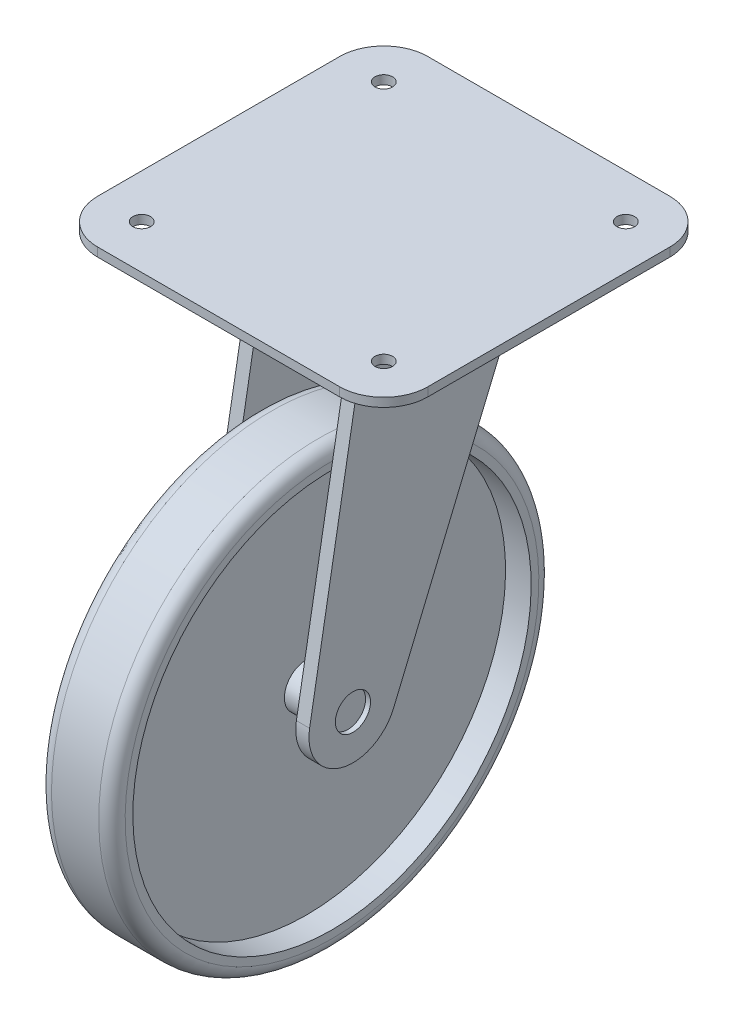
SolidWorks part; units mm, degrees
ref_plane "Front Plane" through (0, 0, 0) normal (0, 0, 1) x (1, 0, 0)
ref_plane "Top Plane" through (0, 0, 0) normal (0, 1, 0) x (1, 0, 0)
ref_plane "Right Plane" through (0, 0, 0) normal (1, 0, 0) x (0, 0, -1)
sketch "Sketch1" plane through (0, 0, 0) normal (0, 1, 0) x (1, 0, 0)
  line L0 (0, -55) -> (0, 55) construction
  line L1 (-37.5, 37.5) -> (37.5, 37.5)
  line L2 (-37.5, 37.5) -> (-37.5, -37.5)
  line L3 (-37.5, -37.5) -> (37.5, -37.5)
  line L4 (37.5, 37.5) -> (37.5, -37.5)
  line L5 (-55, 0) -> (55, 0) construction
  circle A0 centre (27.5, 27.5) radius 2
  circle A1 centre (27.5, -27.5) radius 2
  circle A2 centre (-27.5, -27.5) radius 2
  circle A3 centre (-27.5, 27.5) radius 2
  dimension "D4" = 10
  dimension "D5" = 10
  dimension "D6" = 4
  dimension "D1" = 75
  dimension "D2" = 37.5
  dimension "D3" = 37.5
  dimension "D7" = 4
extrude "Boss-Extrude1" add sketch "Sketch1" against normal blind 2
fillet "Fillet1" radius 10 4 edges at (-37.5, -1, 37.5) (-37.5, -1, -37.5) (37.5, -1, -37.5) (37.5, -1, 37.5)
sketch "Sketch2" plane through (0, -2, 0) normal (0, -1, 0) x (1, 0, 0)
  circle A0 centre (0, 0) radius 21.2583
  circle A1 centre (0, 0) radius 25
  dimension "D1" = 50
extrude "Boss-Extrude2" add sketch "Sketch2" along normal blind 6
sketch "Sketch3" plane through (0, 0, 0) normal (1, 0, 0) x (0, 0, -1)
  line L0 (0, 4.4) -> (0, -4.4) construction
  line L1 (41.25, 0) -> (-41.25, 0) construction
  line L2 (-17.5495, -8) -> (20.9636, -8)
  line L3 (-25, -8) -> (25, -8) construction
  line L4 (20.9636, -8) -> (-10.7749, -83.8596)
  line L5 (-17.5495, -8) -> (-29.8502, -78.2759)
  circle A0 centre (-20, -80) radius 50 construction
  arc A1 (-29.8502, -78.2759) -> (-10.7749, -83.8596) centre (-20, -80) ccw
  circle A2 centre (-20, -80) radius 4
  dimension "D1" = 100
  dimension "D4" = 8
  dimension "D5" = 20
  dimension "D2" = 20
  dimension "D3" = 80
extrude "Boss-Extrude3" add sketch "Sketch3" along normal blind 3 from offset 10
mirror "Mirror1" about plane through (0, 0, 0) normal (1, 0, 0) of "Boss-Extrude3"
ref_plane "Plane1" through (0, 0, 20) normal (0, 0, 1) x (1, 0, 0)
sketch "Sketch4" plane through (0, 0, 20) normal (0, 0, 1) x (1, 0, 0)
  line L0 (-10, -80) -> (11.8719, -80) construction
  line L1 (-13, -80) -> (-10, -80) construction
  line L2 (-10, -90) -> (-10, -78.2759) construction
  line L3 (13, -80) -> (10, -80) construction
  line L4 (2.4272, -34.7483) -> (8.2406, -34.7483)
  line L5 (-12.1181, -80) -> (11.8719, -80)
  line L6 (-12.1181, -80) -> (-12.1181, -75)
  line L7 (-12.1181, -75) -> (-2.6493, -75)
  line L8 (11.8719, -80) -> (11.8719, -75)
  line L10 (-2.6493, -75) -> (-2.6493, -34.7483)
  line L11 (2.4272, -75) -> (11.8719, -75)
  line L12 (2.4272, -75) -> (2.4272, -34.7483)
  line L13 (-5.4977, -30) -> (5.2406, -30)
  line L14 (-8.4977, -33) -> (-8.4977, -34.7483)
  line L15 (-8.4977, -34.7483) -> (-2.6493, -34.7483)
  line L16 (8.2406, -33) -> (8.2406, -34.7483)
  arc A0 (5.2406, -30) -> (8.2406, -33) centre (5.2406, -33) cw
  arc A1 (-5.4977, -30) -> (-8.4977, -33) centre (-5.4977, -33) ccw
  dimension "D1" = 3
  dimension "D2" = 4.7483
  dimension "D3" = 5
  dimension "D4" = 50
revolve "Revolve1" add sketch "Sketch4" angle 360 about L0
